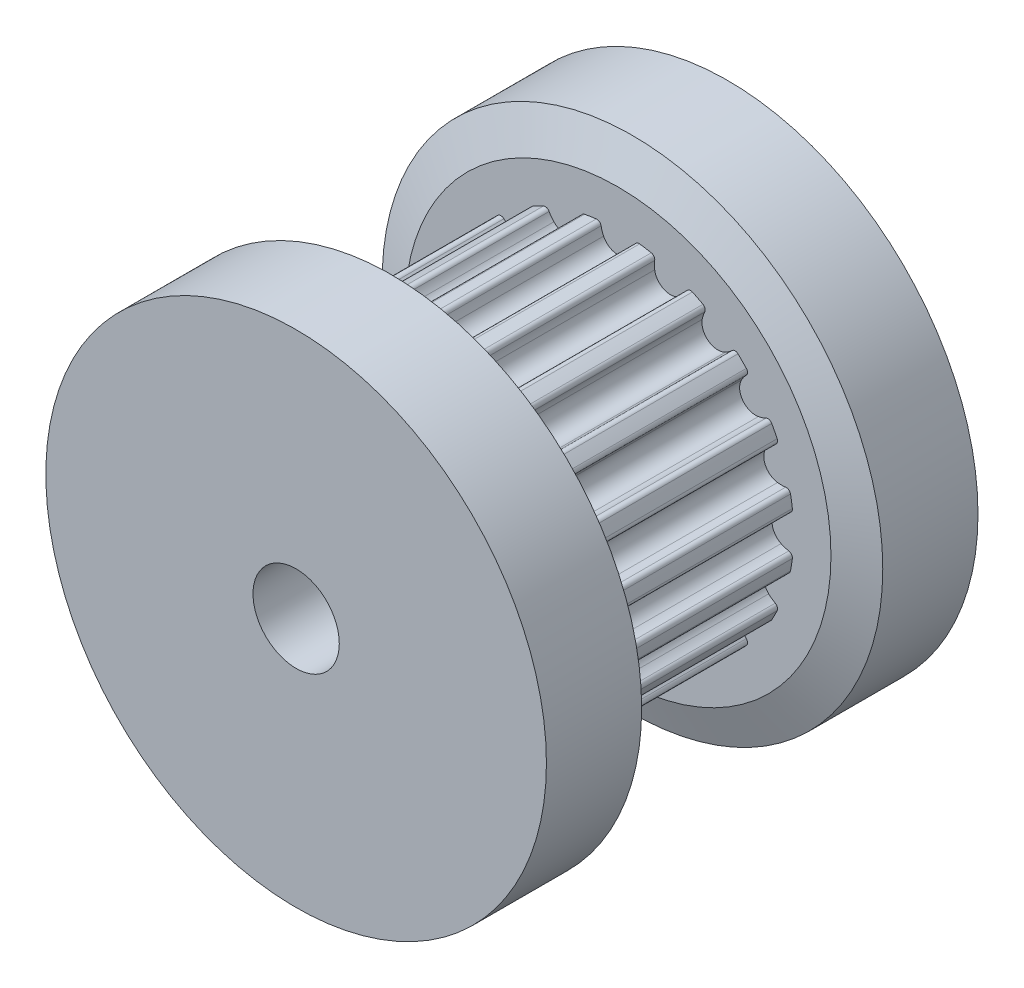
SolidWorks part; units mm, degrees
ref_plane "Front Plane" through (0, 0, 0) normal (0, 0, 1) x (1, 0, 0)
ref_plane "Top Plane" through (0, 0, 0) normal (0, 1, 0) x (1, 0, 0)
ref_plane "Right Plane" through (0, 0, 0) normal (1, 0, 0) x (0, 0, -1)
sketch "Sketch1" plane through (0, 0, 0) normal (0, 0, 1) x (1, 0, 0)
  point P0 (-2.841, 8.6995)
  line B0 (-1.7499, 5.3585) -> (1.7499, 5.3585) construction
  line B1 (0, 0) -> (0, 5.3585) construction
  line B2 (0, 5.3585) -> (0, 11.2111) construction
  line B3 (0, 6.3625) -> (1.9751, 6.0482) construction
  line B4 (1.9751, 6.0482) -> (2.6648, 5.8229) construction
  line B5 (1.9751, 6.0482) -> (1.7499, 5.3585) construction
  line B6 (-1.9751, 6.0482) -> (-1.7499, 5.3585) construction
  line B7 (-1.8963, 5.8067) -> (-2.841, 8.6995)
  line B8 (-2.841, 8.6995) -> (2.841, 8.6995)
  line B9 (2.841, 8.6995) -> (1.8963, 5.8067)
  circle B10 centre (0, 0) radius 6.3625 construction
  circle B11 centre (0, 0) radius 8.6995 construction
  circle B12 centre (0, 0) radius 6.1085 construction
  arc B13 (-0.4989, 5.6703) -> (0.4989, 5.6703) centre (0, 5.9135) ccw
  arc B14 (-0.4989, 5.6703) -> (-0.5855, 5.9387) centre (0.4, 6.1085) cw
  arc B15 (-1.8963, 5.8067) -> (-0.7518, 6.0621) centre (0, 0) cw
  arc B16 (-0.5855, 5.9387) -> (-0.7518, 6.0621) centre (-0.7333, 5.9132) ccw
  arc B17 (1.8963, 5.8067) -> (0.7518, 6.0621) centre (0, 0) ccw
  arc B18 (0.5855, 5.9387) -> (0.7518, 6.0621) centre (0.7333, 5.9132) cw
  arc B19 (0.4989, 5.6703) -> (0.5855, 5.9387) centre (-0.4, 6.1085) ccw
sketch_block_instance "Block-Gt Timing Belt Pulley Groove-1"
sketch_block "Block-Gt Timing Belt Pulley Groove" parameters "D1"=12.725, "D2"=17.399, "D6"=0.555, "D7"=1, "D9"=0.15, "D3"=9.6972, "D4"=4.8486, "D5"=2, "D8"=0.254, "D10"=0.4, "D11"=0.75
sketch "Sketch2" plane through (0, 0, 0) normal (1, 0, 0) x (0, 0, -1)
  line L0 (-3.685, 6.1085) -> (3.685, 6.1085)
  line L1 (-7.5, 0) -> (7.5, 0) construction
  line L2 (-3.685, 6.1085) -> (-3.685, 7.404)
  line L3 (-3.685, 7.404) -> (-4.19, 8.6995)
  line L4 (-4.19, 8.6995) -> (-7.5, 8.6995)
  line L5 (-7.5, 8.6995) -> (-7.5, 0)
  line L6 (3.685, 6.1085) -> (3.685, 7.404)
  line L7 (3.685, 7.404) -> (4.19, 8.6995)
  line L8 (4.19, 8.6995) -> (7.5, 8.6995)
  line L9 (7.5, 8.6995) -> (7.5, 0)
  line L10 (0, 6.1085) -> (0, 0) construction
  line L11 (-7.5, 0) -> (7.5, 0)
  point P5 (4.5366, 10.1881)
  point P9 (3.685, 8.0015)
  point P13 (0, 0)
  dimension "D1" = 12.217
  dimension "D2" = 7.37
  dimension "D3" = 8.38
  dimension "D4" = 17.399
  dimension "D5" = 14.808
  dimension "D6" = 15
revolve "Revolve1" add sketch "Sketch2" angle 360 about L11
sketch "Sketch5" plane through (0, 0, 0) normal (0, 0, 1) x (1, 0, 0)
  line L0 (2.841, 8.6995) -> (1.8963, 5.8067) construction
  line L1 (-1.8963, 5.8067) -> (-2.841, 8.6995) construction
  line L2 (-2.841, 8.6995) -> (2.841, 8.6995) construction
  line L3 (2.841, 8.6995) -> (1.8963, 5.8067)
  line L4 (-1.8963, 5.8067) -> (-2.841, 8.6995)
  line L5 (-2.841, 8.6995) -> (2.841, 8.6995)
  arc A0 (1.8963, 5.8067) -> (0.7518, 6.0621) centre (0, 0) ccw construction
  arc A1 (0.7518, 6.0621) -> (0.5855, 5.9387) centre (0.7333, 5.9132) ccw construction
  arc A2 (0.4989, 5.6703) -> (0.5855, 5.9387) centre (-0.4, 6.1085) ccw construction
  arc A3 (-0.4989, 5.6703) -> (0.4989, 5.6703) centre (0, 5.9135) ccw construction
  arc A4 (-0.5855, 5.9387) -> (-0.4989, 5.6703) centre (0.4, 6.1085) ccw construction
  arc A5 (-0.5855, 5.9387) -> (-0.7518, 6.0621) centre (-0.7333, 5.9132) ccw construction
  arc A6 (-0.7518, 6.0621) -> (-1.8963, 5.8067) centre (0, 0) ccw construction
  arc A7 (1.8963, 5.8067) -> (0.7518, 6.0621) centre (0, 0) ccw
  arc A8 (0.7518, 6.0621) -> (0.5855, 5.9387) centre (0.7333, 5.9132) ccw
  arc A9 (0.4989, 5.6703) -> (0.5855, 5.9387) centre (-0.4, 6.1085) ccw
  arc A10 (-0.4989, 5.6703) -> (0.4989, 5.6703) centre (0, 5.9135) ccw
  arc A11 (-0.5855, 5.9387) -> (-0.4989, 5.6703) centre (0.4, 6.1085) ccw
  arc A12 (-0.5855, 5.9387) -> (-0.7518, 6.0621) centre (-0.7333, 5.9132) ccw
  arc A13 (-0.7518, 6.0621) -> (-1.8963, 5.8067) centre (0, 0) ccw
extrude "Cut-Extrude1" cut sketch "Sketch5" against normal up to surface (3.685 mm away) and the other way up to surface (3.685 mm away) up to face at (6.1085, 0, -3.685) other way up to face at (7.404, 0, 3.685)
pattern_circular "CirPattern1" count 20 over 360 about axis through (0, 0, 0) along (0, 0, 1) of "Cut-Extrude1"
sketch "Sketch6" plane through (0, 0, 7.5) normal (0, 0, 1) x (1, 0, 0)
  circle A0 centre (0, 0) radius 1.5
  dimension "D1" = 3
extrude "Cut-Extrude2" cut sketch "Sketch6" against normal through all
